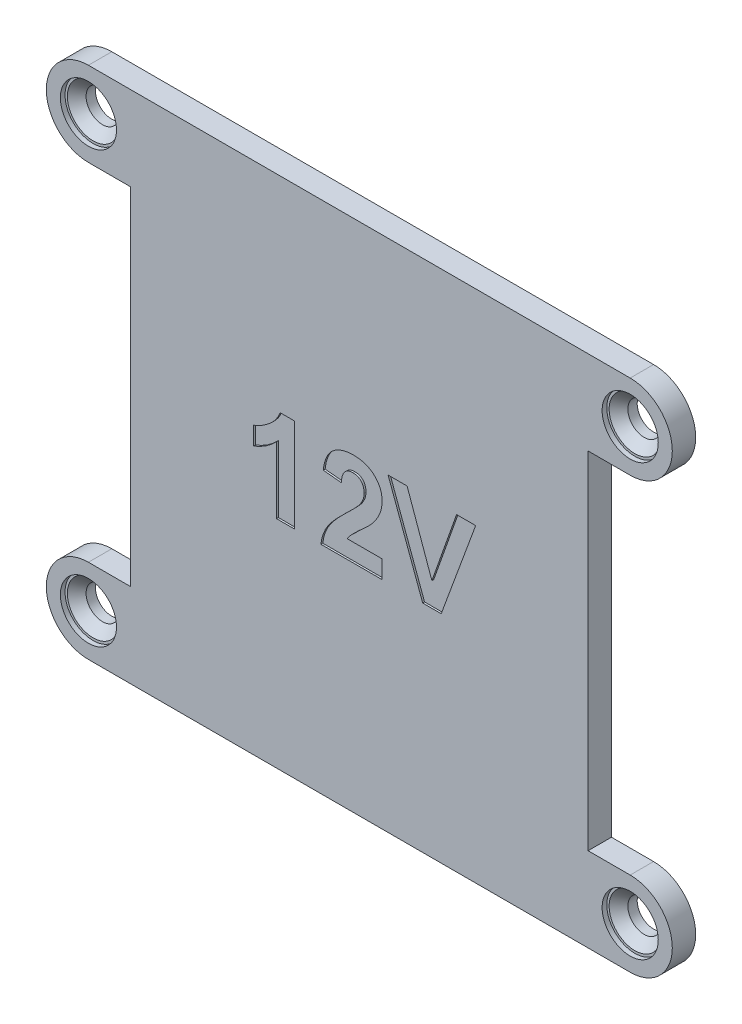
SolidWorks part; units mm, degrees
ref_plane "Front Plane" through (0, 0, 0) normal (0, 0, 1) x (1, 0, 0)
ref_plane "Top Plane" through (0, 0, 0) normal (0, 1, 0) x (1, 0, 0)
ref_plane "Right Plane" through (0, 0, 0) normal (1, 0, 0) x (0, 0, -1)
sketch "Sketch1" plane through (0, 0, 0) normal (0, 0, 1) x (1, 0, 0)
  line L0 (-20.75, 27.5) -> (20.75, 27.5)
  line L1 (-20.75, -27.5) -> (20.75, -27.5)
  line L10 (-22.95, 16.6) -> (-20.75, 16.6)
  line L11 (-20.75, 16.6) -> (-20.75, 27.5)
  line L12 (-20.75, 27.5) -> (-28.95, 27.5)
  line L13 (-28.95, 18.5) -> (-24.45, 18.5)
  line L14 (-24.45, 18.5) -> (-24.45, -18.5)
  line L15 (-24.45, -18.5) -> (-28.95, -18.5)
  line L16 (-28.95, -27.5) -> (-20.75, -27.5)
  line L17 (-20.75, -27.5) -> (-20.75, -16.6)
  line L18 (-20.75, -16.6) -> (-22.95, -16.6)
  line L19 (-22.95, -16.6) -> (-22.95, 16.6)
  line L20 (-22.95, 16.6) -> (-20.75, 16.6)
  line L21 (-20.75, 16.6) -> (-20.75, 27.5)
  line L22 (-20.75, 27.5) -> (-28.95, 27.5)
  line L23 (-28.95, 18.5) -> (-24.45, 18.5)
  line L24 (-24.45, 18.5) -> (-24.45, -18.5)
  line L25 (-24.45, -18.5) -> (-28.95, -18.5)
  line L26 (-28.95, -27.5) -> (-20.75, -27.5)
  line L27 (-20.75, -27.5) -> (-20.75, -16.6)
  line L28 (-20.75, -16.6) -> (-22.95, -16.6)
  line L29 (-22.95, -16.6) -> (-22.95, 16.6)
  line L30 (20.75, 27.5) -> (20.75, 16.6)
  line L31 (20.75, 16.6) -> (22.95, 16.6)
  line L32 (22.95, 16.6) -> (22.95, -16.6)
  line L33 (22.95, -16.6) -> (20.75, -16.6)
  line L34 (20.75, -16.6) -> (20.75, -27.5)
  line L35 (20.75, -27.5) -> (28.95, -27.5)
  line L36 (28.95, -18.5) -> (24.45, -18.5)
  line L37 (24.45, -18.5) -> (24.45, 18.5)
  line L38 (24.45, 18.5) -> (28.95, 18.5)
  line L39 (28.95, 27.5) -> (20.75, 27.5)
  line L40 (20.75, 27.5) -> (20.75, 16.6)
  line L41 (20.75, 16.6) -> (22.95, 16.6)
  line L42 (22.95, 16.6) -> (22.95, -16.6)
  line L43 (22.95, -16.6) -> (20.75, -16.6)
  line L44 (20.75, -16.6) -> (20.75, -27.5)
  line L45 (20.75, -27.5) -> (28.95, -27.5)
  line L46 (28.95, -18.5) -> (24.45, -18.5)
  line L47 (24.45, -18.5) -> (24.45, 18.5)
  line L48 (24.45, 18.5) -> (28.95, 18.5)
  line L49 (28.95, 27.5) -> (20.75, 27.5)
  circle A0 centre (28.95, 23) radius 1.75 construction
  circle A1 centre (28.95, -23) radius 1.75 construction
  arc A2 (-28.95, 27.5) -> (-28.95, 18.5) centre (-28.95, 23) ccw
  arc A3 (-28.95, -18.5) -> (-28.95, -27.5) centre (-28.95, -23) ccw
  arc A4 (-28.95, 27.5) -> (-28.95, 18.5) centre (-28.95, 23) ccw
  arc A5 (-28.95, -18.5) -> (-28.95, -27.5) centre (-28.95, -23) ccw
  arc A6 (28.95, -27.5) -> (28.95, -18.5) centre (28.95, -23) ccw
  arc A7 (28.95, 18.5) -> (28.95, 27.5) centre (28.95, 23) ccw
  arc A8 (28.95, -27.5) -> (28.95, -18.5) centre (28.95, -23) ccw
  arc A9 (28.95, 18.5) -> (28.95, 27.5) centre (28.95, 23) ccw
  circle A10 centre (-28.95, -23) radius 1.75 construction
  circle A11 centre (-28.95, 23) radius 1.75 construction
  circle A12 centre (28.95, 23) radius 1.75
  circle A13 centre (28.95, -23) radius 1.75
  circle A14 centre (-28.95, -23) radius 1.75
  circle A15 centre (-28.95, 23) radius 1.75
  dimension "D1" = 0
  dimension "D2" = 0
extrude "Boss-Extrude1" add sketch "Sketch1" along normal blind 2.5 contours L25 A5 L26 L27 L28 L29 L20 L21 L22 A4 L23 L24 | L44 L43 L42 L41 L40 L0 L21 L20 L29 L28 L27 L1 | L48 A9 L49 L40 L41 L42 L43 L44 L45 A8 L46 L47
sketch "Sketch4" plane through (0, 0, 2.5) normal (0, 0, 1) x (1, 0, 0)
  line L0 (-24.45, -4.4145) -> (24.45, -4.4145) construction
  line L1 (-24.45, 18.5) -> (-24.45, -18.5) construction
  line L2 (24.45, -18.5) -> (24.45, 18.5) construction
  text T0 "12V" font "Arial" height 10
extrude "Cut-Extrude1" cut sketch "Sketch4" against normal blind 0.2
sketch "Sketch5" plane through (0, 0, 2.5) normal (0, 0, 1) x (1, 0, 0)
  circle A0 centre (-28.95, 23) radius 3
  circle A1 centre (28.95, 23) radius 3
  circle A2 centre (28.95, -23) radius 3
  circle A3 centre (-28.95, -23) radius 3
  dimension "D1" = 6
extrude "Cut-Extrude2" cut sketch "Sketch5" against normal blind 0.5
chamfer "Chamfer2" distance 1 angle 45 4 edges at (-27.2, -23, 2) (30.7, -23, 2) (30.7, 23, 2) (-27.2, 23, 2)
